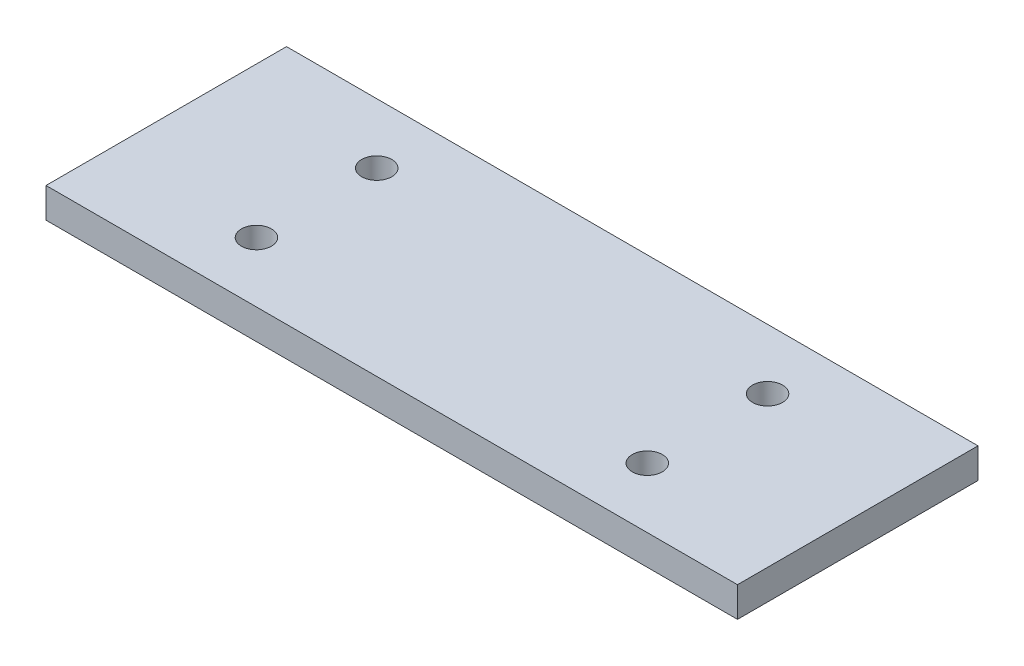
SolidWorks part; units mm, degrees
ref_plane "Front Plane" through (0, 0, 0) normal (0, 0, 1) x (1, 0, 0)
ref_plane "Top Plane" through (0, 0, 0) normal (0, 1, 0) x (1, 0, 0)
ref_plane "Right Plane" through (0, 0, 0) normal (1, 0, 0) x (0, 0, -1)
sketch "Sketch2" plane through (0, 0, 0) normal (0, 1, 0) x (1, 0, 0)
  line L1 (0, 0) -> (115, 0)
  line L2 (0, 0) -> (0, 40)
  line L3 (0, 40) -> (115, 40)
  line L4 (115, 0) -> (115, 40)
  circle A0 centre (25, 30) radius 2.5
  circle A1 centre (25, 10) radius 2.5
  circle A2 centre (90, 10) radius 2.5
  circle A3 centre (90, 30) radius 2.5
  point P10 (0, 0)
  point P11 (0, 0)
  point P15 (0, 0)
  dimension "D3" = 10
  dimension "D5" = 5
  dimension "D1" = 115
  dimension "D2" = 40
  dimension "D4" = 20
  dimension "D6" = 25
  dimension "D7" = 65
extrude "Boss-Extrude1" add sketch "Sketch2" along normal blind 5
